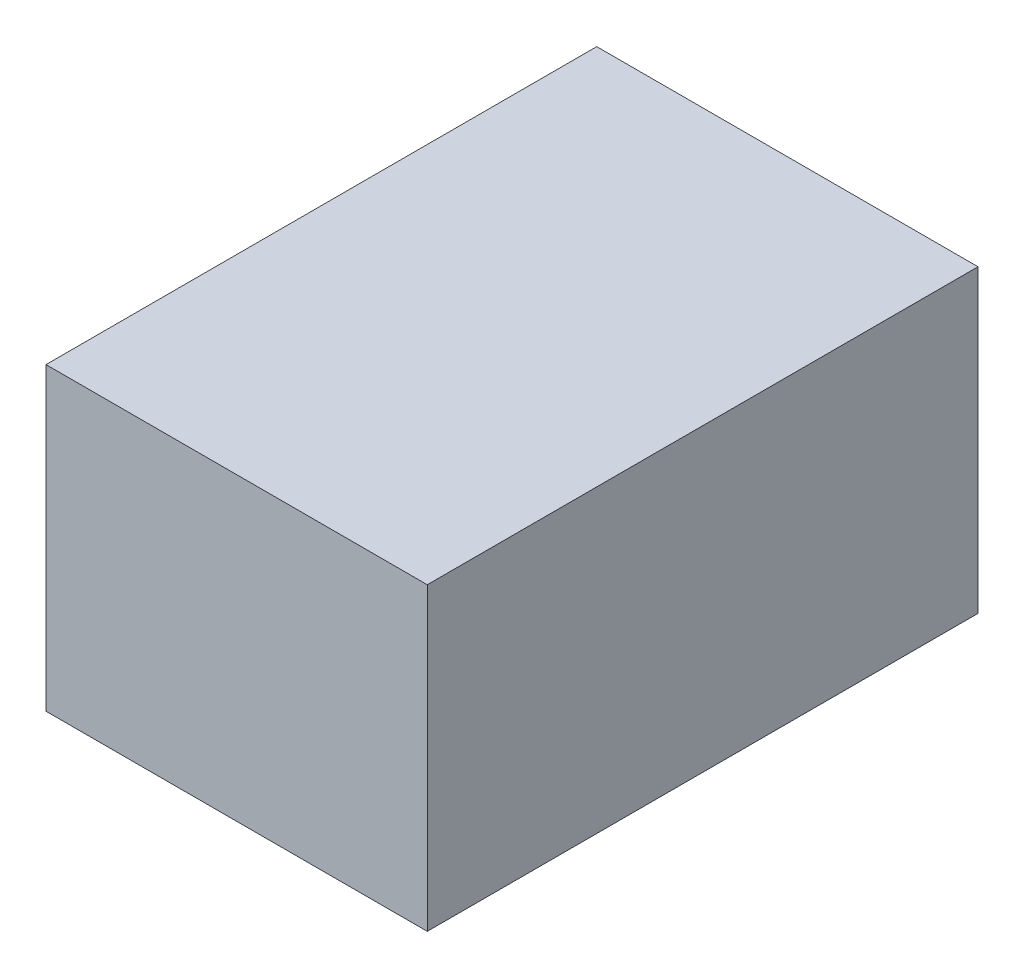
SolidWorks part; units mm, degrees
ref_plane "Front Plane" through (0, 0, 0) normal (0, 0, 1) x (1, 0, 0)
ref_plane "Top Plane" through (0, 0, 0) normal (0, 1, 0) x (1, 0, 0)
ref_plane "Right Plane" through (0, 0, 0) normal (1, 0, 0) x (0, 0, -1)
sketch "Sketch2" plane through (0, 0, 0) normal (0, 1, 0) x (1, 0, 0)
  line L1 (11.43, -16.51) -> (-11.43, -16.51)
  line L2 (11.43, -16.51) -> (11.43, 16.51)
  line L3 (11.43, 16.51) -> (-11.43, 16.51)
  line L4 (-11.43, -16.51) -> (-11.43, 16.51)
  line L5 (11.43, -16.51) -> (-11.43, 16.51) construction
  line L6 (11.43, 16.51) -> (-11.43, -16.51) construction
  point P0 (0, 0)
  dimension "D1" = 22.86
  dimension "D2" = 33.02
extrude "Boss-Extrude1" add sketch "Sketch2" along normal blind 18
